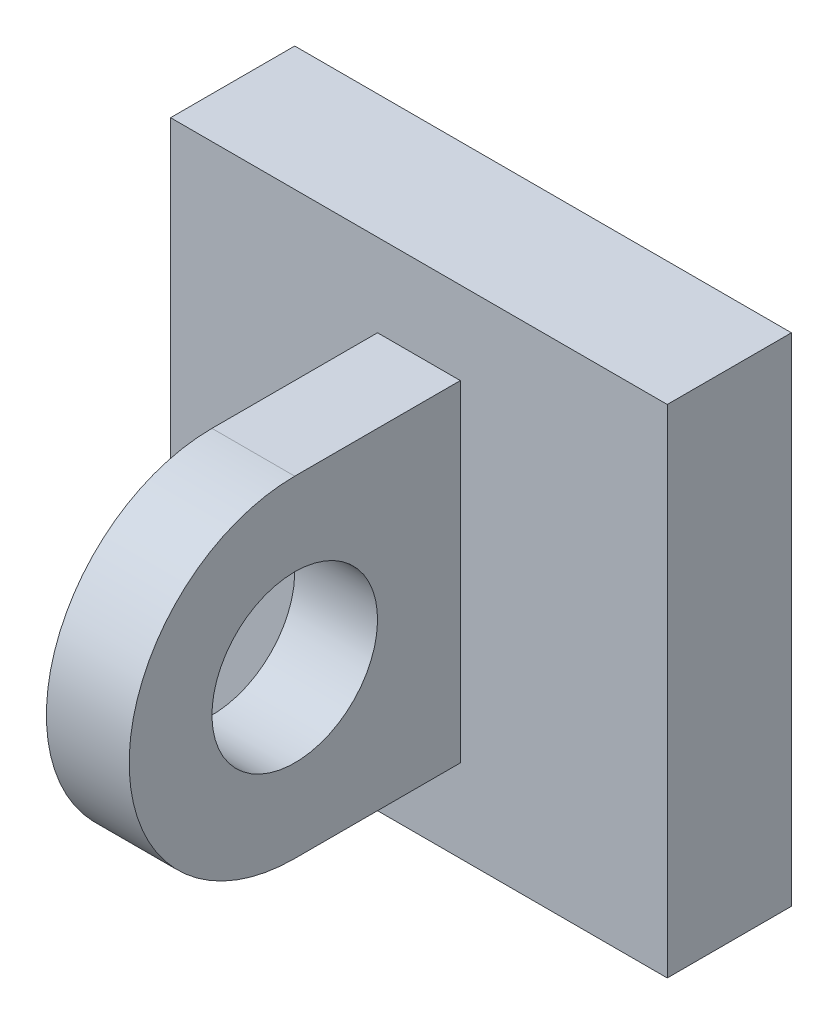
SolidWorks part; units mm, degrees
ref_plane "Front Plane" through (0, 0, 0) normal (0, 0, 1) x (1, 0, 0)
ref_plane "Top Plane" through (0, 0, 0) normal (0, 1, 0) x (1, 0, 0)
ref_plane "Right Plane" through (0, 0, 0) normal (1, 0, 0) x (0, 0, -1)
sketch "Sketch1" plane through (0, 0, 0) normal (0, 0, 1) x (1, 0, 0)
  line L1 (-30, 30) -> (30, 30)
  line L2 (-30, 30) -> (-30, -30)
  line L3 (-30, -30) -> (30, -30)
  line L4 (30, 30) -> (30, -30)
  line L5 (-30, 30) -> (30, -30) construction
  line L6 (-30, -30) -> (30, 30) construction
  point P0 (0, 0)
  dimension "D1" = 60
  dimension "D2" = 60
extrude "Boss-Extrude1" add sketch "Sketch1" along normal mid plane 15
ref_plane "Plane1" through (0, 0, 0) normal (1, 0, 0) x (0, 0, -1)
sketch "Sketch3" plane through (0, 0, 0) normal (1, 0, 0) x (0, 0, -1)
  line L1 (-27.5, -20) -> (-7.5, -20)
  line L2 (-27.5, -20) -> (-27.5, 20)
  line L3 (-27.5, 20) -> (-7.5, 20)
  line L4 (-7.5, -20) -> (-7.5, 20)
  line L5 (-27.5, -20) -> (-7.5, 20) construction
  line L6 (-27.5, 20) -> (-7.5, -20) construction
  line L7 (-7.5, -30) -> (-7.5, 30) construction
  circle A1 centre (-27.5, 0) radius 10
  arc A2 (-27.5, 20) -> (-27.5, -20) centre (-27.5, 0) ccw
  point P0 (-17.5, 0)
  point P5 (-7.5, 0)
  point P11 (-7.5, 0)
  dimension "D3" = 20
  dimension "D1" = 20
  dimension "D2" = 40
extrude "Boss-Extrude2" add sketch "Sketch3" along normal mid plane 10 contours A1 L2 L1 L4 L3 | L2 A2 A1
